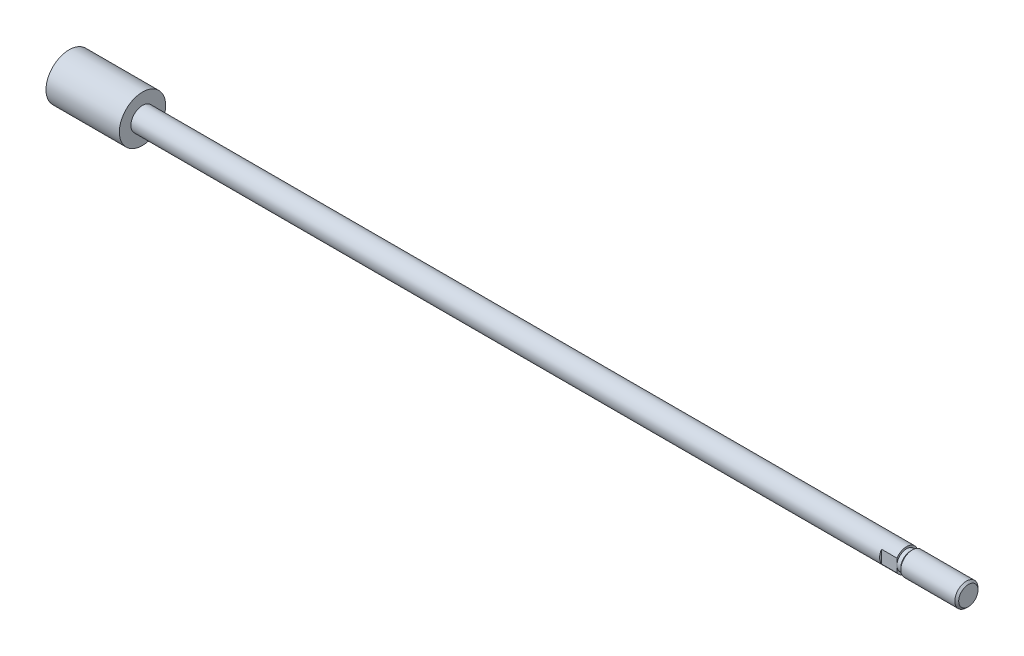
SolidWorks part; units mm, degrees
material "Wrought Stainless Steel"
ref_plane "Front Plane" through (0, 0, 0) normal (0, 0, 1) x (1, 0, 0)
ref_plane "Top Plane" through (0, 0, 0) normal (0, 1, 0) x (1, 0, 0)
ref_plane "Right Plane" through (0, 0, 0) normal (1, 0, 0) x (0, 0, -1)
sketch "Sketch1" plane through (0, 0, 0) normal (0, 0, 1) x (1, 0, 0)
  line L0 (-26.3912, 0) -> (0, 0) construction
  line L1 (0, -6) -> (0, 0)
  line L2 (19, -3) -> (217, -3)
  line L3 (233, -3) -> (233, 0)
  line L4 (0, 0) -> (233, 0)
  line L5 (217, -3) -> (217, -2.5)
  line L6 (217, -2.5) -> (218, -2.5)
  line L7 (218, -2.5) -> (218.5, -3)
  line L8 (218.5, -3) -> (233, -3)
  line L10 (212, -6.5) -> (212, 6.5) construction
  line L11 (0, -6) -> (19, -6)
  line L14 (19, -3) -> (19, -6)
  dimension "D1" = 1
  dimension "D2" = 45
  dimension "OD" = 6
  dimension "D3" = 3
  dimension "D4" = 2.5
  dimension "D5" = 21
  dimension "D6" = 16
  dimension "D7" = 233
  dimension "piton L" = 19
  dimension "piston od" = 12
revolve "Revolve1" add sketch "Sketch1" angle 360 about L0
cosmetic thread "Cosmetic Thread1" parameters "D2"=5
chamfer "Chamfer1" distance 0.5 angle 45 1 edges at (233, 0, 3)
sketch "Sketch2" plane through (217, 0, 0) normal (1, 0, 0) x (0, 0, -1)
  line L0 (0, 0) -> (0, 14.809) construction
  line L1 (-6, 6) -> (-2.5, 6)
  line L2 (-6, 6) -> (-6, -6)
  line L3 (-6, -6) -> (-2.5, -6)
  line L4 (-2.5, 6) -> (-2.5, -6)
  line L5 (0, 55) -> (0, -55) construction
  circle A0 centre (0, 0) radius 6 construction
  dimension "D1" = 5
extrude "Cut-Extrude1" cut sketch "Sketch2" against normal blind 4
mirror "Mirror1" about plane through (0, 0, 0) normal (0, 0, 1) of "Cut-Extrude1"
